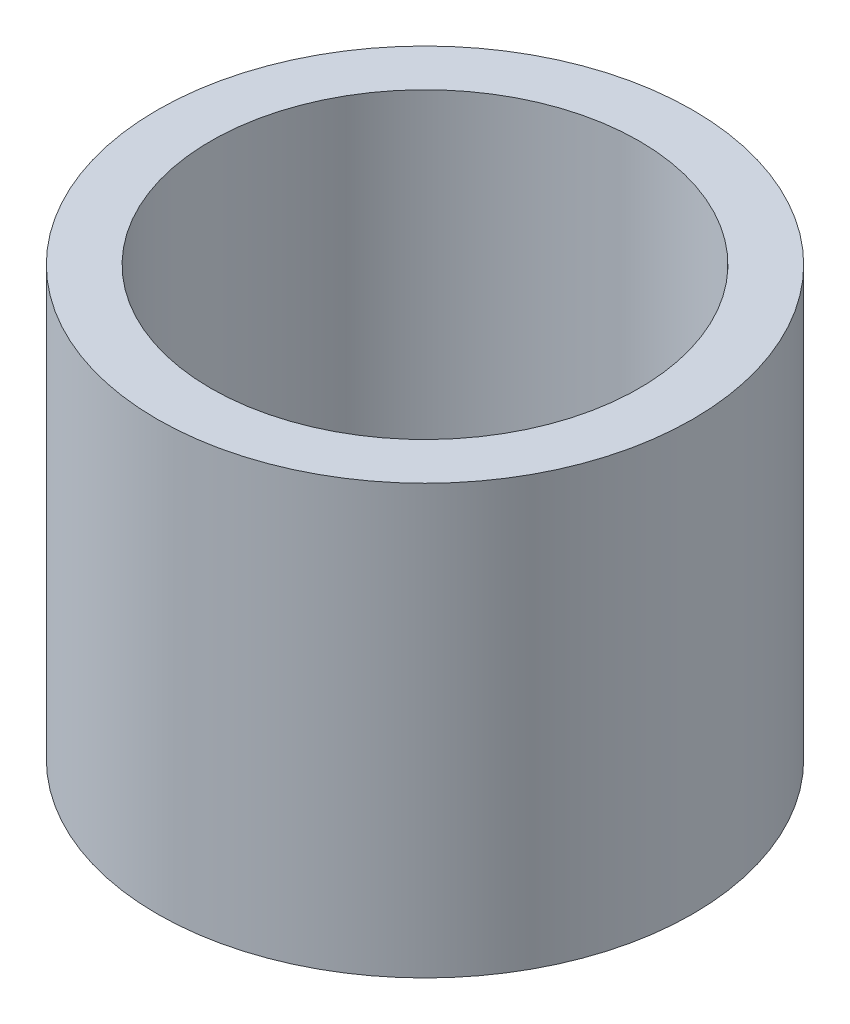
SolidWorks part; units mm, degrees
material "Bronce de aluminio"
ref_plane "Alzado" through (0, 0, 0) normal (0, 0, 1) x (1, 0, 0)
ref_plane "Planta" through (0, 0, 0) normal (0, 1, 0) x (1, 0, 0)
ref_plane "Vista lateral" through (0, 0, 0) normal (1, 0, 0) x (0, 0, -1)
sketch "Croquis1" plane through (0, 0, 0) normal (0, 1, 0) x (1, 0, 0)
  circle A0 centre (0, 0) radius 7.5
  circle A1 centre (0, 0) radius 6
extrude "Saliente-Extruir1" add sketch "Croquis1" along normal blind 12
scale "Escala1" scale about centroid uniform scaling yes scale factor 7
